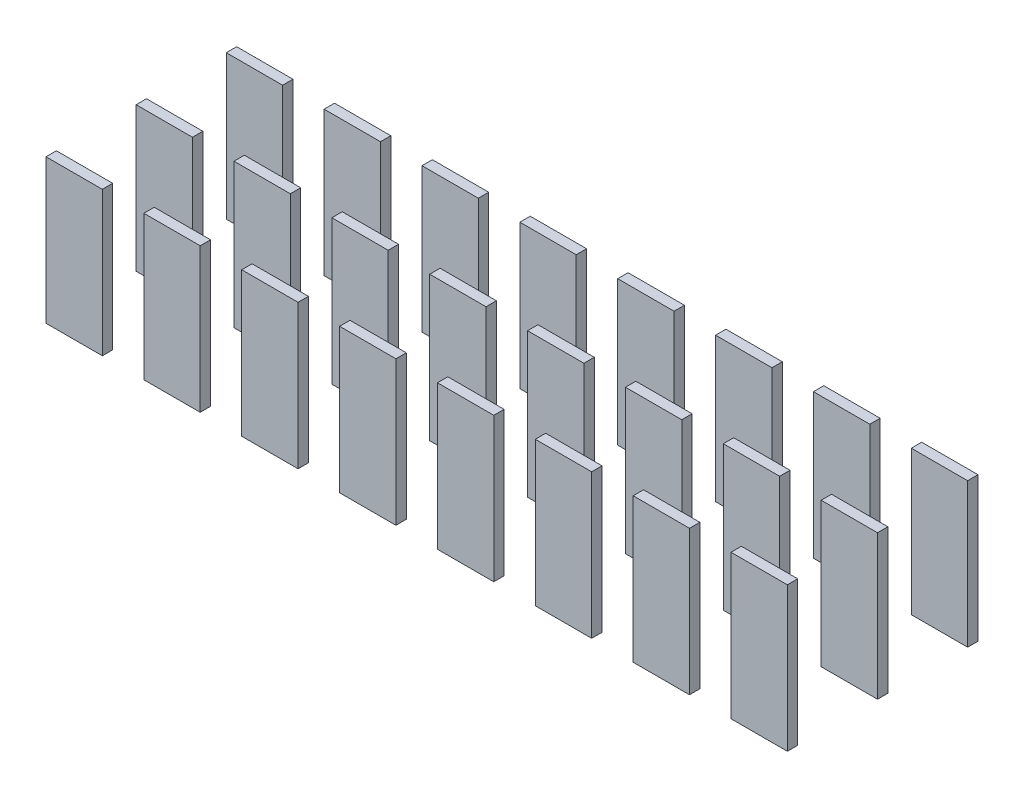
SolidWorks part; units mm, degrees
ref_plane "Front Plane" through (0, 0, 0) normal (0, 0, 1) x (1, 0, 0)
ref_plane "Top Plane" through (0, 0, 0) normal (0, 1, 0) x (1, 0, 0)
ref_plane "Right Plane" through (0, 0, 0) normal (1, 0, 0) x (0, 0, -1)
sketch "Sketch1" plane through (0, 0, 0) normal (0, 1, 0) x (1, 0, 0)
  line L0 (5.5154, 0) -> (8.6904, 0)
  line L1 (0, 0) -> (3.175, 0)
  line L2 (0, 0) -> (0, 0.5842)
  line L3 (0, 0.5842) -> (3.175, 0.5842)
  line L4 (3.175, 0) -> (3.175, 0.5842)
  line L5 (5.5154, 0) -> (5.5154, 0.5842)
  line L6 (5.5154, 0.5842) -> (8.6904, 0.5842)
  line L7 (8.6904, 0) -> (8.6904, 0.5842)
  line L8 (11.0309, 0) -> (14.2059, 0)
  line L9 (11.0309, 0) -> (11.0309, 0.5842)
  line L10 (11.0309, 0.5842) -> (14.2059, 0.5842)
  line L11 (14.2059, 0) -> (14.2059, 0.5842)
  line L12 (16.5463, 0) -> (19.7213, 0)
  line L13 (16.5463, 0) -> (16.5463, 0.5842)
  line L14 (16.5463, 0.5842) -> (19.7213, 0.5842)
  line L15 (19.7213, 0) -> (19.7213, 0.5842)
  line L16 (22.0617, 0) -> (25.2367, 0)
  line L17 (22.0617, 0) -> (22.0617, 0.5842)
  line L18 (22.0617, 0.5842) -> (25.2367, 0.5842)
  line L19 (25.2367, 0) -> (25.2367, 0.5842)
  line L20 (27.5771, 0) -> (30.7521, 0)
  line L21 (27.5771, 0) -> (27.5771, 0.5842)
  line L22 (27.5771, 0.5842) -> (30.7521, 0.5842)
  line L23 (30.7521, 0) -> (30.7521, 0.5842)
  line L24 (33.0926, 0) -> (36.2676, 0)
  line L25 (33.0926, 0) -> (33.0926, 0.5842)
  line L26 (33.0926, 0.5842) -> (36.2676, 0.5842)
  line L27 (36.2676, 0) -> (36.2676, 0.5842)
  line L28 (38.608, 0) -> (41.783, 0)
  line L29 (38.608, 0) -> (38.608, 0.5842)
  line L30 (38.608, 0.5842) -> (41.783, 0.5842)
  line L31 (41.783, 0) -> (41.783, 0.5842)
  line L32 (5.5154, 5.08) -> (8.6904, 5.08)
  line L33 (0, 5.08) -> (3.175, 5.08)
  line L34 (0, 5.08) -> (0, 5.6642)
  line L35 (0, 5.6642) -> (3.175, 5.6642)
  line L36 (3.175, 5.08) -> (3.175, 5.6642)
  line L37 (5.5154, 5.08) -> (5.5154, 5.6642)
  line L38 (5.5154, 5.6642) -> (8.6904, 5.6642)
  line L39 (8.6904, 5.08) -> (8.6904, 5.6642)
  line L40 (11.0309, 5.08) -> (14.2059, 5.08)
  line L41 (11.0309, 5.08) -> (11.0309, 5.6642)
  line L42 (11.0309, 5.6642) -> (14.2059, 5.6642)
  line L43 (14.2059, 5.08) -> (14.2059, 5.6642)
  line L44 (16.5463, 5.08) -> (19.7213, 5.08)
  line L45 (16.5463, 5.08) -> (16.5463, 5.6642)
  line L46 (16.5463, 5.6642) -> (19.7213, 5.6642)
  line L47 (19.7213, 5.08) -> (19.7213, 5.6642)
  line L48 (22.0617, 5.08) -> (25.2367, 5.08)
  line L49 (22.0617, 5.08) -> (22.0617, 5.6642)
  line L50 (22.0617, 5.6642) -> (25.2367, 5.6642)
  line L51 (25.2367, 5.08) -> (25.2367, 5.6642)
  line L52 (27.5771, 5.08) -> (30.7521, 5.08)
  line L53 (27.5771, 5.08) -> (27.5771, 5.6642)
  line L54 (27.5771, 5.6642) -> (30.7521, 5.6642)
  line L55 (30.7521, 5.08) -> (30.7521, 5.6642)
  line L56 (33.0926, 5.08) -> (36.2676, 5.08)
  line L57 (33.0926, 5.08) -> (33.0926, 5.6642)
  line L58 (33.0926, 5.6642) -> (36.2676, 5.6642)
  line L59 (36.2676, 5.08) -> (36.2676, 5.6642)
  line L60 (38.608, 5.08) -> (41.783, 5.08)
  line L61 (38.608, 5.08) -> (38.608, 5.6642)
  line L62 (38.608, 5.6642) -> (41.783, 5.6642)
  line L63 (41.783, 5.08) -> (41.783, 5.6642)
  line L64 (5.5154, 10.16) -> (8.6904, 10.16)
  line L65 (0, 10.16) -> (3.175, 10.16)
  line L66 (0, 10.16) -> (0, 10.7442)
  line L67 (0, 10.7442) -> (3.175, 10.7442)
  line L68 (3.175, 10.16) -> (3.175, 10.7442)
  line L69 (5.5154, 10.16) -> (5.5154, 10.7442)
  line L70 (5.5154, 10.7442) -> (8.6904, 10.7442)
  line L71 (8.6904, 10.16) -> (8.6904, 10.7442)
  line L72 (11.0309, 10.16) -> (14.2059, 10.16)
  line L73 (11.0309, 10.16) -> (11.0309, 10.7442)
  line L74 (11.0309, 10.7442) -> (14.2059, 10.7442)
  line L75 (14.2059, 10.16) -> (14.2059, 10.7442)
  line L76 (16.5463, 10.16) -> (19.7213, 10.16)
  line L77 (16.5463, 10.16) -> (16.5463, 10.7442)
  line L78 (16.5463, 10.7442) -> (19.7213, 10.7442)
  line L79 (19.7213, 10.16) -> (19.7213, 10.7442)
  line L80 (22.0617, 10.16) -> (25.2367, 10.16)
  line L81 (22.0617, 10.16) -> (22.0617, 10.7442)
  line L82 (22.0617, 10.7442) -> (25.2367, 10.7442)
  line L83 (25.2367, 10.16) -> (25.2367, 10.7442)
  line L84 (27.5771, 10.16) -> (30.7521, 10.16)
  line L85 (27.5771, 10.16) -> (27.5771, 10.7442)
  line L86 (27.5771, 10.7442) -> (30.7521, 10.7442)
  line L87 (30.7521, 10.16) -> (30.7521, 10.7442)
  line L88 (33.0926, 10.16) -> (36.2676, 10.16)
  line L89 (33.0926, 10.16) -> (33.0926, 10.7442)
  line L90 (33.0926, 10.7442) -> (36.2676, 10.7442)
  line L91 (36.2676, 10.16) -> (36.2676, 10.7442)
  line L92 (38.608, 10.16) -> (41.783, 10.16)
  line L93 (38.608, 10.16) -> (38.608, 10.7442)
  line L94 (38.608, 10.7442) -> (41.783, 10.7442)
  line L95 (41.783, 10.16) -> (41.783, 10.7442)
  dimension "D1" = 3.175
  dimension "D2" = 0.5842
  dimension "D4" = 38.608
  dimension "D3" = 8
  dimension "D5" = 3
extrude "Boss-Extrude1" add sketch "Sketch1" along normal blind 8.128
